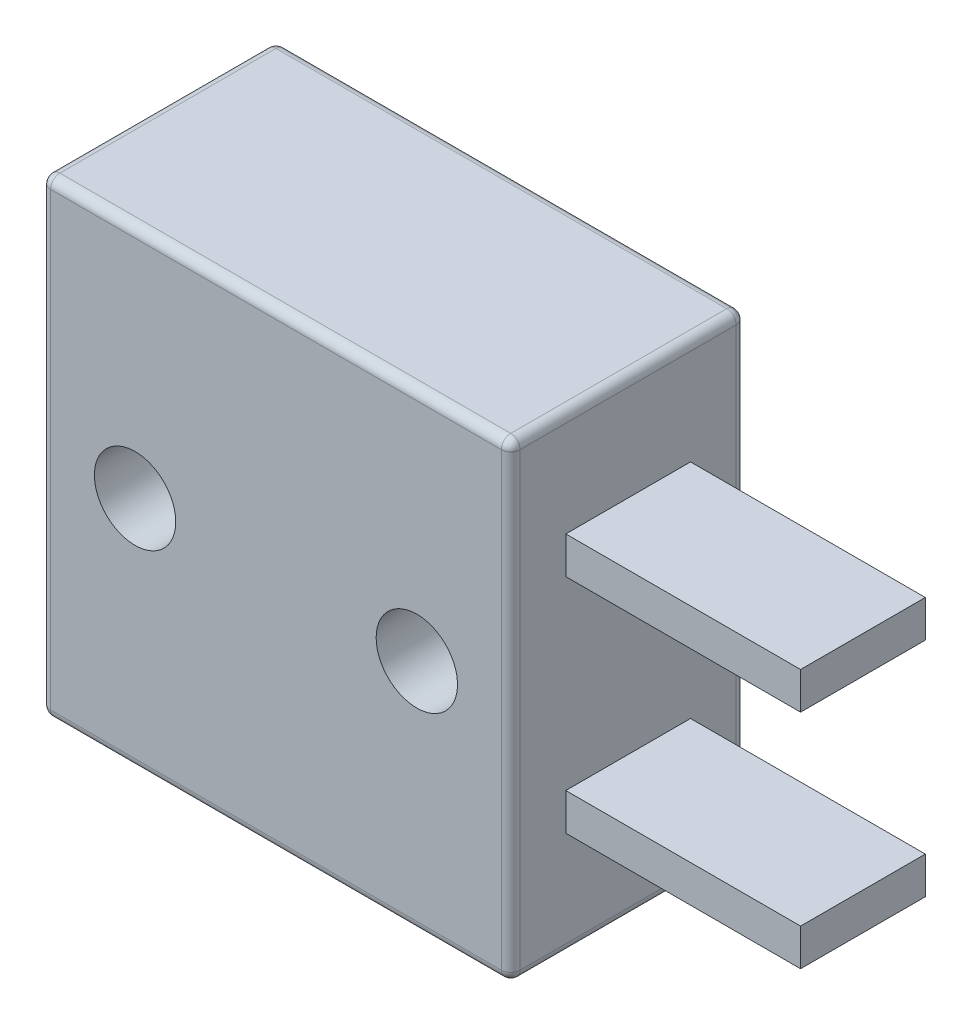
SolidWorks part; units mm, degrees
material "Copper"
ref_plane "Front Plane" through (0, 0, 0) normal (0, 0, 1) x (1, 0, 0)
ref_plane "Top Plane" through (0, 0, 0) normal (0, 1, 0) x (1, 0, 0)
ref_plane "Right Plane" through (0, 0, 0) normal (1, 0, 0) x (0, 0, -1)
sketch "Sketch1" plane through (0, 0, 0) normal (0, 0, 1) x (1, 0, 0)
  line L0 (-3.81, 0) -> (0, 0) construction
  line L1 (-6.35, 6.35) -> (6.35, 6.35)
  line L2 (-6.35, 6.35) -> (-6.35, -6.35)
  line L3 (-6.35, -6.35) -> (6.35, -6.35)
  line L4 (6.35, 6.35) -> (6.35, -6.35)
  line L5 (-6.35, 6.35) -> (6.35, -6.35) construction
  line L6 (-6.35, -6.35) -> (6.35, 6.35) construction
  line L7 (0, 0) -> (0, -6.35) construction
  circle A0 centre (-3.81, 0) radius 1.1
  circle A1 centre (3.81, 0) radius 1.1
  point P0 (0, 0)
  dimension "D3" = 2.2
  dimension "D1" = 12.7
  dimension "D2" = 12.7
  dimension "D4" = 2.54
extrude "Boss-Extrude1" add sketch "Sketch1" along normal blind 6.35
ref_plane "Plane1" through (0, 0, 3.175) normal (0, 0, 1) x (1, 0, 0)
sketch "Sketch2" plane through (0, 0, 3.175) normal (0, 0, 1) x (1, 0, 0)
  line L0 (6.35, -6.35) -> (6.35, 6.35) construction
  line L1 (6.35, -6.35) -> (6.35, 6.35) construction
  line L3 (6.35, 3.5048) -> (12.7, 3.5048)
  line L4 (6.35, 3.5048) -> (6.35, 2.5048)
  line L5 (6.35, 2.5048) -> (12.7, 2.5048)
  line L6 (12.7, 3.5048) -> (12.7, 2.5048)
  line L7 (6.35, 6.35) -> (-6.35, 6.35) construction
  line L8 (0, 0) -> (6.35, 0) construction
  line L9 (12.7, -3.5048) -> (12.7, -2.5048)
  line L10 (6.35, -2.5048) -> (12.7, -2.5048)
  line L11 (6.35, -3.5048) -> (6.35, -2.5048)
  line L12 (6.35, -3.5048) -> (12.7, -3.5048)
  dimension "D1" = 1
  dimension "D2" = 6.35
  dimension "D3" = 2.8452
extrude "Boss-Extrude2" add sketch "Sketch2" along normal mid plane 3.3734
fillet "Fillet1" radius 0.254 12 edges at (-6.35, 0, 0) (-6.35, -6.35, 3.175) (0, -6.35, 0) (6.35, 0, 0) (6.35, -6.35, 3.175) (0, -6.35, 6.35) (6.35, 0, 6.35) (-6.35, 0, 6.35) (-6.35, 6.35, 3.175) (0, 6.35, 0) (6.35, 6.35, 3.175) (0, 6.35, 6.35)
